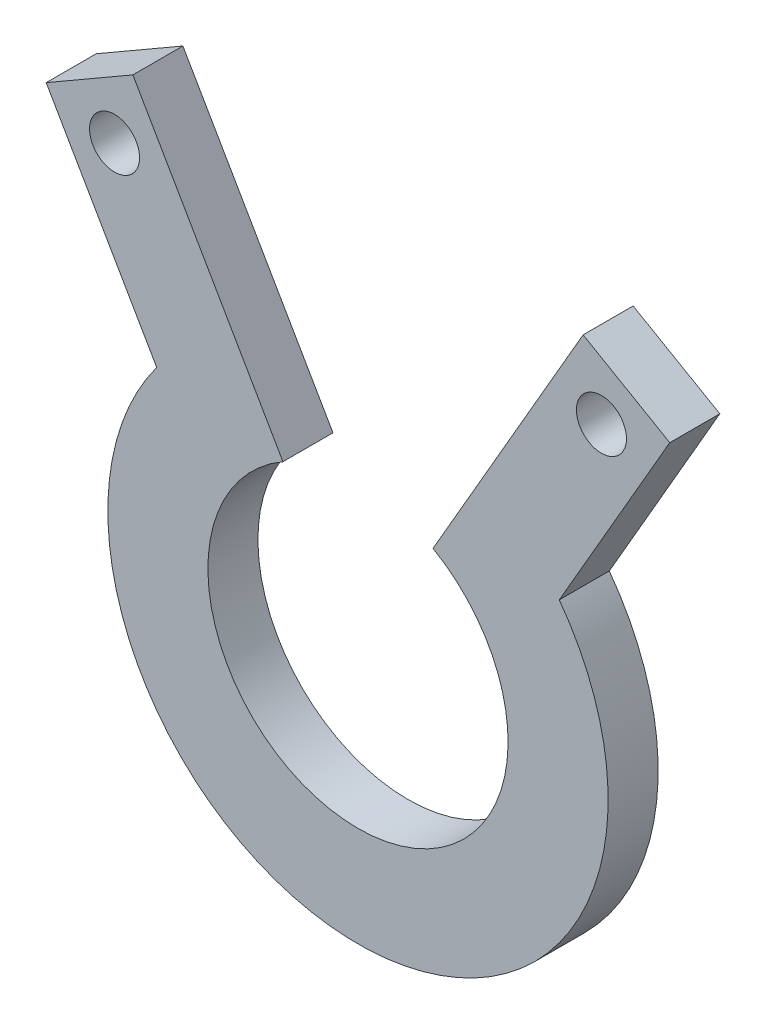
SolidWorks part; units mm, degrees
ref_plane "Front Plane" through (0, 0, 0) normal (0, 0, 1) x (1, 0, 0)
ref_plane "Top Plane" through (0, 0, 0) normal (0, 1, 0) x (1, 0, 0)
ref_plane "Right Plane" through (0, 0, 0) normal (1, 0, 0) x (0, 0, -1)
sketch "Sketch2" plane through (0, 0, 0) normal (0, 0, 1) x (1, 0, 0)
  circle A0 centre (0, 0) radius 12.7
  circle A1 centre (0, 0) radius 15.875
  circle A2 centre (0, 0) radius 9.525
  dimension "D1" = 25.4
  dimension "D2" = 3.175
  dimension "D3" = 3.175
extrude "Boss-Extrude1" add sketch "Sketch2" along normal blind 3.175 contours A1 A0 | A0 A2
sketch "Sketch3" plane through (0, 0, 3.175) normal (0, 0, 1) x (1, 0, 0)
  line L0 (-17.0371, 23.1592) -> (-15.4496, 20.4095) construction
  line L1 (0, 0) -> (-7.9375, 13.7482) construction
  line L2 (0, 0) -> (0, 15.875) construction
  line L3 (-7.9375, 13.7482) -> (-14.2875, 24.7467)
  line L4 (-14.2875, 24.7467) -> (-19.7868, 21.5717)
  line L5 (-19.7868, 21.5717) -> (-12.7741, 9.4254)
  line L6 (-14.2875, 24.7467) -> (-7.2748, 12.6004)
  line L7 (-13.4368, 10.5732) -> (-19.7868, 21.5717)
  line L8 (17.0371, 23.1592) -> (15.4496, 20.4095) construction
  line L9 (13.4368, 10.5732) -> (19.7868, 21.5717)
  line L10 (14.2875, 24.7467) -> (7.2748, 12.6004)
  line L11 (19.7868, 21.5717) -> (12.7741, 9.4254)
  line L12 (14.2875, 24.7467) -> (19.7868, 21.5717)
  line L13 (7.9375, 13.7482) -> (14.2875, 24.7467)
  circle A0 centre (0, 0) radius 15.875 construction
  circle A2 centre (-15.4496, 20.4095) radius 1.5875
  circle A3 centre (15.4496, 20.4095) radius 1.5875
  circle M7 centre (0, 0) radius 15.875
  dimension "D5" = 3.175
  dimension "D1" = 30
  dimension "D2" = 3.175
  dimension "D3" = 12.7
  dimension "D4" = 6.35
extrude "Boss-Extrude2" add sketch "Sketch3" against normal up to surface (3.175 mm away) contours L4 L5 L3 A2 M7 | L12 L10 L11 L9 A3 M7 up to face at (15.875, 0, 0)
ref_plane "Plane4" through (-14.2875, 24.7467, 3.175) normal (0, 0, 1) x (1, 0, 0)
sketch "Sketch5" plane through (0, 0, 3.175) normal (0, 0, 1) x (1, 0, 0)
  line L0 (-7.9375, 13.7482) -> (0, 0)
  line L1 (0, 0) -> (7.9375, 13.7482)
  arc A0 (7.9375, 13.7482) -> (-7.9375, 13.7482) centre (0, 0) ccw construction
  arc A1 (7.9375, 13.7482) -> (-7.9375, 13.7482) centre (0, 0) ccw
extrude "Cut-Extrude1" cut sketch "Sketch5" against normal up to surface (3.175 mm away) up to face at (0, 14.4763, 0)
